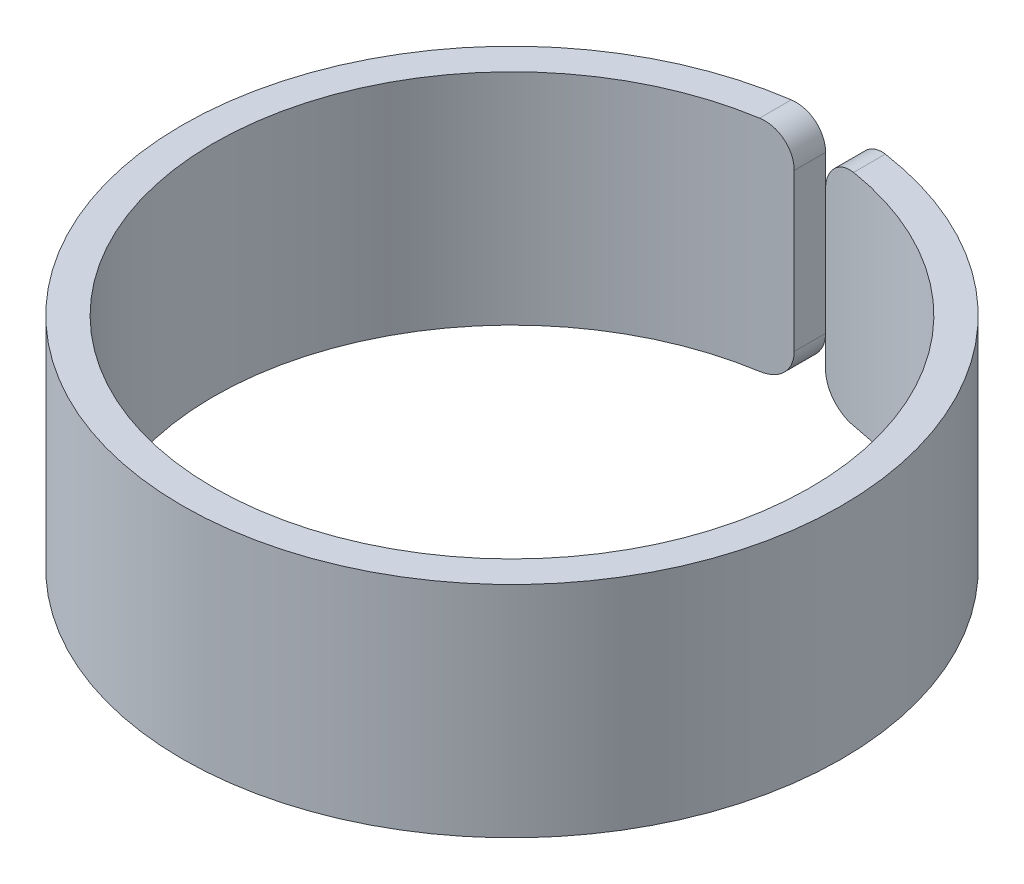
SolidWorks part; units mm, degrees
ref_plane "Front Plane" through (0, 0, 0) normal (0, 0, 1) x (1, 0, 0)
ref_plane "Top Plane" through (0, 0, 0) normal (0, 1, 0) x (1, 0, 0)
ref_plane "Right Plane" through (0, 0, 0) normal (1, 0, 0) x (0, 0, -1)
sketch "Sketch3" plane through (0, 0, 0) normal (0, 1, 0) x (1, 0, 0)
  circle A0 centre (0, 0) radius 9.52
  point P4 (0, 0)
  point P5 (0.3031, 9.02)
  dimension "D1" = 19.04
extrude "Extrude-Thin1" add sketch "Sketch3" along normal mid plane 7 thin
sketch "Sketch4" plane through (0, 0, 0) normal (0, 1, 0) x (1, 0, 0)
  line L5 (0.5, 0) -> (-0.5, 0)
  line L6 (0.5, 0) -> (0.5, 1000)
  line L7 (0.5, 1000) -> (-0.5, 1000)
  line L8 (-0.5, 0) -> (-0.5, 1000)
  circle A1 centre (0, 0) radius 10.52 construction
  point P4 (0, 0)
  dimension "D1" = 1
  dimension "D2" = 1000
extrude "Cut-Extrude1" cut sketch "Sketch4" against normal through all both and the other way through all
fillet "Fillet1" radius 1 4 edges at (0.5, 3.5, -10.0075) (-0.5, 3.5, -10.0075) (-0.5, -3.5, -10.0075) (0.5, -3.5, -10.0075)
